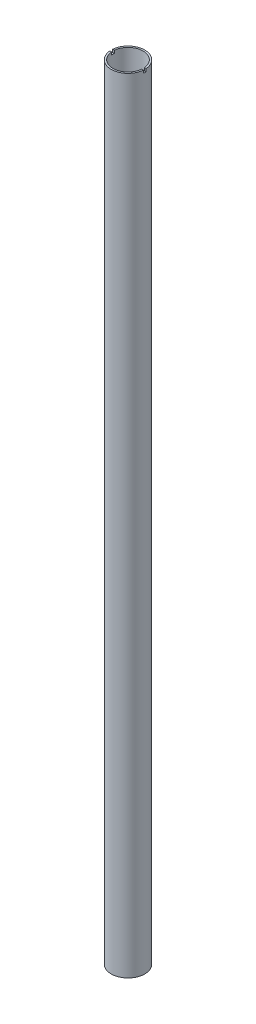
SolidWorks part; units mm, degrees
ref_plane "Front Plane" through (0, 0, 0) normal (0, 0, 1) x (1, 0, 0)
ref_plane "Top Plane" through (0, 0, 0) normal (0, 1, 0) x (1, 0, 0)
ref_plane "Right Plane" through (0, 0, 0) normal (1, 0, 0) x (0, 0, -1)
sketch "Sketch1" plane through (0, 0, 0) normal (0, 1, 0) x (1, 0, 0)
  circle A0 centre (0, 0) radius 15
  circle A1 centre (0, 0) radius 13.5
  dimension "D1" = 1.5
  dimension "D2" = 30
extrude "Boss-Extrude1" add sketch "Sketch1" along normal blind 700
ref_plane "Plane1" through (0, 0, 50) normal (0, 0, 1) x (1, 0, 0)
sketch "Sketch2" plane through (0, 700, 0) normal (0, 1, 0) x (1, 0, 0)
  line L1 (-15, -1.25) -> (15, -1.25)
  line L2 (-15, -1.25) -> (-15, 1.25)
  line L3 (-15, 1.25) -> (15, 1.25)
  line L4 (15, -1.25) -> (15, 1.25)
  line L5 (-15, -1.25) -> (15, 1.25) construction
  line L6 (-15, 1.25) -> (15, -1.25) construction
  circle A0 centre (0, 0) radius 15 construction
  point P0 (0, 0)
  dimension "D1" = 2.5
extrude "Cut-Extrude1" cut sketch "Sketch2" against normal blind 2.5
